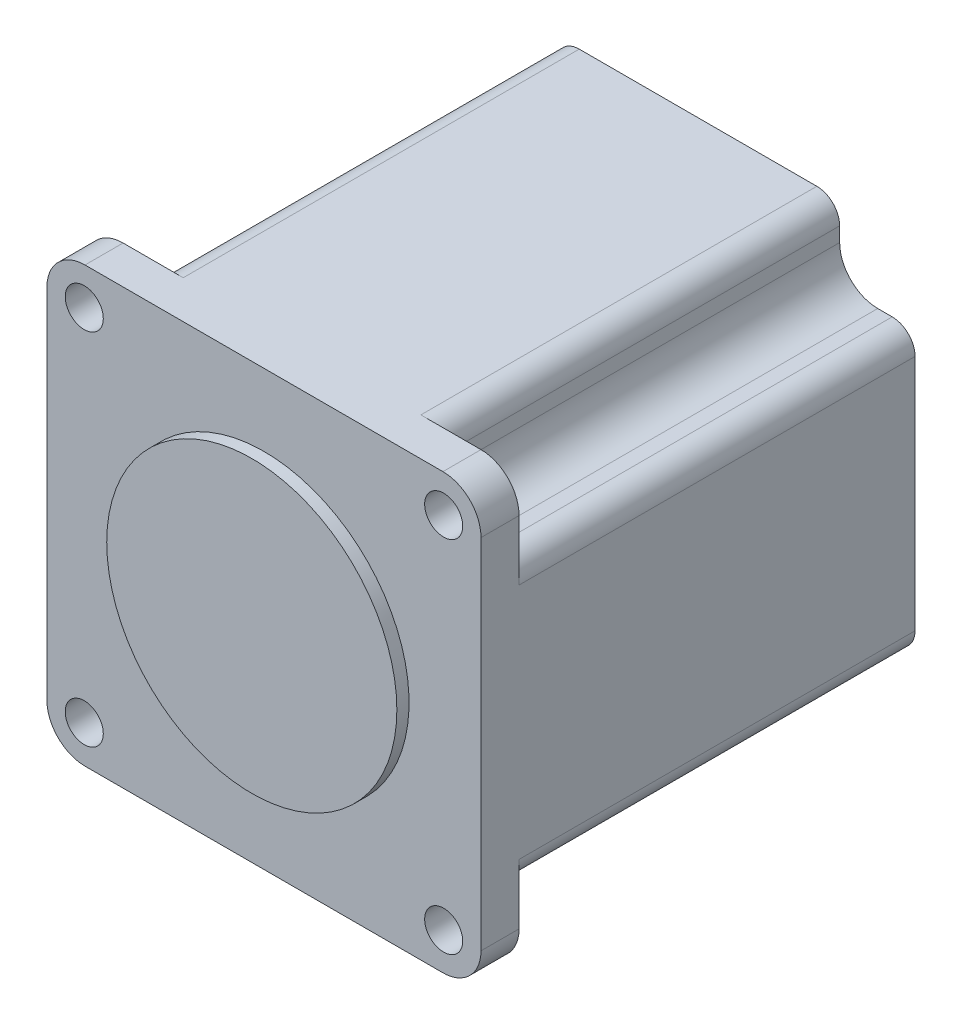
SolidWorks part; units mm, degrees
ref_plane "Front Plane" through (0, 0, 0) normal (0, 0, 1) x (1, 0, 0)
ref_plane "Top Plane" through (0, 0, 0) normal (0, 1, 0) x (1, 0, 0)
ref_plane "Right Plane" through (0, 0, 0) normal (1, 0, 0) x (0, 0, -1)
sketch "Sketch1" plane through (0, 0, 0) normal (0, 0, 1) x (1, 0, 0)
  line L1 (-23.5, -28.5) -> (23.5, -28.5)
  line L2 (-28.5, -23.5) -> (-28.5, 23.5)
  line L3 (-23.5, 28.5) -> (23.5, 28.5)
  line L4 (28.5, -23.5) -> (28.5, 23.5)
  line L5 (-28.5, -28.5) -> (28.5, 28.5) construction
  line L6 (-28.5, 28.5) -> (28.5, -28.5) construction
  line L11 (-23.57, -23.57) -> (23.57, 23.57) construction
  line L12 (-23.57, 23.57) -> (23.57, -23.57) construction
  arc A0 (-23.5, -28.5) -> (-28.5, -23.5) centre (-23.5, -23.5) cw
  arc A1 (23.5, -28.5) -> (28.5, -23.5) centre (23.5, -23.5) ccw
  arc A2 (23.5, 28.5) -> (28.5, 23.5) centre (23.5, 23.5) cw
  arc A3 (-23.5, 28.5) -> (-28.5, 23.5) centre (-23.5, 23.5) ccw
  point P0 (0, 0)
  point P18 (0, 0)
  dimension "D3" = 5
  dimension "D1" = 57
  dimension "D2" = 57
extrude "Boss-Extrude1" add sketch "Sketch1" along normal mid plane 5
sketch "Sketch5" plane through (0, 0, 2.5) normal (0, 0, 1) x (1, 0, 0)
  line L1 (-23.6, -23.6) -> (23.6, -23.6) construction
  line L2 (-23.6, -23.6) -> (-23.6, 23.6) construction
  line L3 (-23.6, 23.6) -> (23.6, 23.6) construction
  line L4 (23.6, -23.6) -> (23.6, 23.6) construction
  line L5 (-23.6, -23.6) -> (23.6, 23.6) construction
  line L6 (-23.6, 23.6) -> (23.6, -23.6) construction
  circle A0 centre (-23.6, 23.6) radius 2.5
  circle A1 centre (23.6, 23.6) radius 2.5
  circle A2 centre (23.6, -23.6) radius 2.5
  circle A3 centre (-23.6, -23.6) radius 2.5
  point P0 (0, 0)
  dimension "D3" = 5
  dimension "D4" = 5
  dimension "D5" = 5
  dimension "D6" = 5
  dimension "D1" = 47.2
  dimension "D2" = 47.2
extrude "Cut-Extrude1" cut sketch "Sketch5" against normal through all
sketch "Sketch3" plane through (0, 0, 2.5) normal (0, 0, 1) x (1, 0, 0)
  circle A0 centre (0, 0) radius 19.05
  dimension "D1" = 38.1
extrude "Boss-Extrude3" add sketch "Sketch3" along normal blind 1.6
sketch "Sketch4" plane through (0, 0, -2.5) normal (0, 0, -1) x (-1, 0, 0)
  line L0 (-18.6, 23.6) -> (-18.6, 25.5)
  line L1 (-23.5, 28.5) -> (23.5, 28.5) construction
  line L2 (-15.6, 28.5) -> (15.6, 28.5)
  line L3 (18.6, 25.5) -> (18.6, 23.6)
  line L4 (23.6, 18.6) -> (25.5, 18.6)
  line L5 (28.5, 23.5) -> (28.5, -23.5) construction
  line L6 (28.5, 15.6) -> (28.5, -15.6)
  line L7 (25.5, -18.6) -> (23.6, -18.6)
  line L8 (18.6, -23.6) -> (18.6, -25.5)
  line L9 (23.5, -28.5) -> (-23.5, -28.5) construction
  line L10 (15.6, -28.5) -> (-15.6, -28.5)
  line L11 (-18.6, -25.5) -> (-18.6, -23.6)
  line L12 (-23.6, -18.6) -> (-25.5, -18.6)
  line L13 (-28.5, -23.5) -> (-28.5, 23.5) construction
  line L14 (-28.5, -15.6) -> (-28.5, 15.6)
  line L15 (-25.5, 18.6) -> (-23.6, 18.6)
  arc A0 (-23.6, 18.6) -> (-18.6, 23.6) centre (-23.6, 23.6) ccw
  arc A1 (18.6, 23.6) -> (23.6, 18.6) centre (23.6, 23.6) ccw
  arc A2 (23.6, -18.6) -> (18.6, -23.6) centre (23.6, -23.6) ccw
  arc A3 (-18.6, -23.6) -> (-23.6, -18.6) centre (-23.6, -23.6) ccw
  arc A4 (-28.5, 15.6) -> (-25.5, 18.6) centre (-25.5, 15.6) cw
  arc A5 (-18.6, 25.5) -> (-15.6, 28.5) centre (-15.6, 25.5) cw
  arc A6 (15.6, 28.5) -> (18.6, 25.5) centre (15.6, 25.5) cw
  arc A7 (28.5, 15.6) -> (25.5, 18.6) centre (25.5, 15.6) ccw
  arc A8 (28.5, -15.6) -> (25.5, -18.6) centre (25.5, -15.6) cw
  arc A9 (15.6, -28.5) -> (18.6, -25.5) centre (15.6, -25.5) ccw
  arc A10 (-15.6, -28.5) -> (-18.6, -25.5) centre (-15.6, -25.5) cw
  arc A11 (-25.5, -18.6) -> (-28.5, -15.6) centre (-25.5, -15.6) cw
  circle A12 centre (23.6, 23.6) radius 2.5 construction
  circle A13 centre (-23.6, 23.6) radius 2.5 construction
  circle A14 centre (23.6, -23.6) radius 2.5 construction
  circle A15 centre (-23.6, -23.6) radius 2.5 construction
  point P7 (-28.5, 18.6)
  point P37 (-18.6, 28.5)
  point P40 (18.6, 28.5)
  point P43 (28.5, 18.6)
  point P46 (28.5, -18.6)
  point P49 (18.6, -28.5)
  point P52 (-18.6, -28.5)
  point P55 (-28.5, -18.6)
  dimension "D1" = 10
  dimension "D2" = 10
  dimension "D3" = 10
  dimension "D4" = 10
  dimension "D5" = 3
extrude "Body" add sketch "Sketch4" along normal blind 52
sketch "Sketch6" [suppressed] plane through (0, 0, -53.5) normal (0, 0, -1) x (-1, 0, 0)
  circle A0 centre (0, 0) radius 3.175
  dimension "D1" = 6.35
extrude "Rear Shaft" [suppressed] add sketch "Sketch6" along normal blind 15
sketch "Sketch7" [suppressed] plane through (0, 0, 2.5) normal (0, 0, 1) x (1, 0, 0)
  circle A0 centre (0, 0) radius 3.175
  dimension "D1" = 6.35
extrude "Front Shaft" [suppressed] add sketch "Sketch7" along normal blind 15
